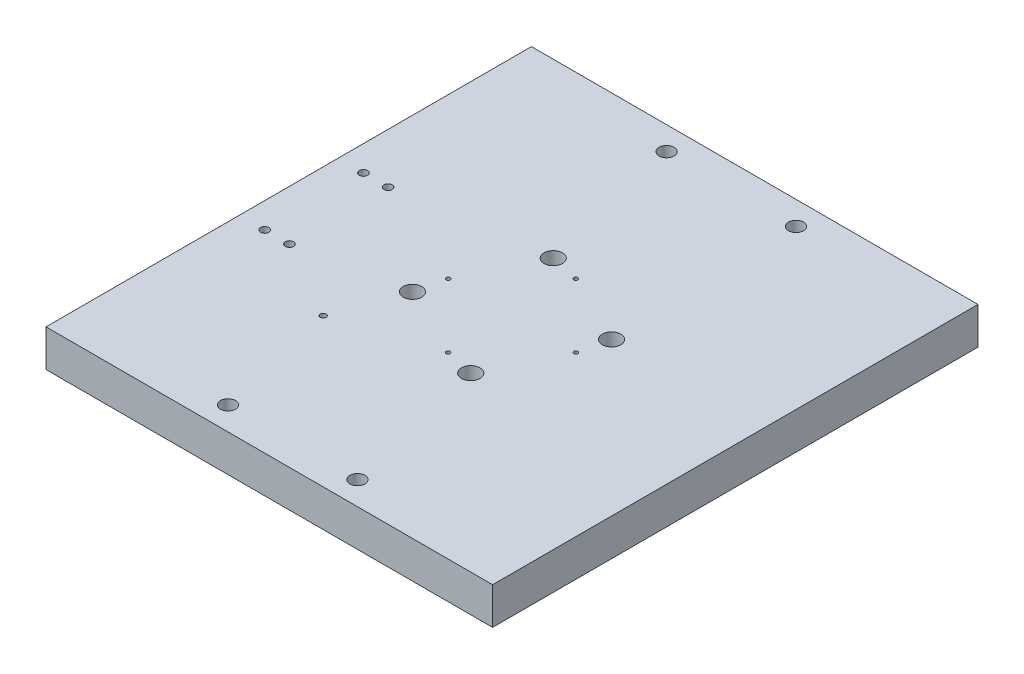
SolidWorks part; units mm, degrees
ref_plane "Front Plane" through (0, 0, 0) normal (0, 0, 1) x (1, 0, 0)
ref_plane "Top Plane" through (0, 0, 0) normal (0, 1, 0) x (1, 0, 0)
ref_plane "Right Plane" through (0, 0, 0) normal (1, 0, 0) x (0, 0, -1)
sketch "Sketch1" plane through (0, 0, 0) normal (0, 1, 0) x (1, 0, 0)
  line L1 (-230, -250) -> (230, -250)
  line L2 (-230, -250) -> (-230, 250)
  line L3 (-230, 250) -> (230, 250)
  line L4 (230, -250) -> (230, 250)
  line L5 (-230, -250) -> (230, 250) construction
  line L6 (-230, 250) -> (230, -250) construction
  point P0 (0, 0)
  dimension "D1" = 500
  dimension "D3" = 0
  dimension "D2" = 460
extrude "Boss-Extrude1" add sketch "Sketch1" along normal blind 38.1
sketch "Sketch3" plane through (0, 38.1, 0) normal (0, 1, 0) x (1, 0, 0)
  line L0 (-230, -250) -> (230, 250) construction
  line L1 (230, -250) -> (-230, 250) construction
  line L2 (0, 0) -> (225.0272, 0) construction
  line L3 (0, 0) -> (0, 160) construction
  line L4 (0, 0) -> (-160, 0) construction
  line L5 (145, 0) -> (145, -15) construction
  line L6 (-145, 0) -> (-145, -23.128) construction
  circle A0 centre (0, 0) radius 145
  circle A1 centre (0, 0) radius 130
  circle A2 centre (0, 0) radius 160
  arc A3 (-130, 0) -> (-160, 0) centre (-145, 0) cw
  arc A4 (130, 0) -> (160, 0) centre (145, 0) ccw
  point P19 (-145, -15)
  dimension "D1" = 15
  dimension "D2" = 15
sketch "Sketch5" plane through (0, 38.1, 0) normal (0, 1, 0) x (1, 0, 0)
  line L0 (65.786, 0) -> (-65.786, 0) construction
  line L1 (0, -124.9952) -> (0, 101.4653) construction
  circle A0 centre (0, 0) radius 65.786
  point P7 (0, -65.786)
  point P8 (0, 65.786)
  dimension "D1" = 131.572
hole_wizard "Tap Drill for M5x0.8 Tap1" positions "Sketch9" profile "Sketch8" hole size "M5x0.8" standard "ANSI Metric"
sketch "Sketch9" plane through (0, 38.1, 0) normal (0, 1, 0) x (1, 0, 0)
  point P0 (0, 65.786)
  point P3 (65.786, 0)
  point P6 (0, -65.786)
  point P9 (-65.786, 0)
sketch "Sketch8" plane through (0, 38.1, -65.786) normal (1, 0, 0) x (0, 0, 1)
  line L0 (0, 0) -> (0, 21.2618)
  line L1 (0, 21.2618) -> (2.1, 20)
  line L2 (2.1, 20) -> (2.1, 0)
  line L5 (2.1, 0) -> (0, 0)
  line L10 (0, 21.2618) -> (-2.1, 20) construction
  line L11 (0, -6.35) -> (0, 107.95) construction
  dimension "Hole Dia." = 4.2
  dimension "Hole Depth" = 20
  dimension "Drill Angle" = 118
sketch "Sketch10" plane through (0, 0, 0) normal (0, -1, 0) x (1, 0, 0)
  line L0 (-72.5116, 30.0353) -> (0, 0) construction
  line L1 (0, 0) -> (72.5116, -30.0353) construction
  line L2 (30.0353, 72.5116) -> (0, 0) construction
  line L3 (0, 0) -> (-30.0353, -72.5116) construction
  line L4 (0, 124.9952) -> (0, -101.4653) construction
  circle A0 centre (0, 0) radius 78.486
  point P3 (0, 78.486)
  point P4 (78.486, 0)
  point P5 (0, -78.486)
  point P6 (-78.486, 0)
  point P7 (-72.5116, 30.0353)
  point P9 (30.0353, 72.5116)
  dimension "D1" = 67.5
  dimension "D3" = 156.972
  dimension "D2" = 22.5
hole_wizard "3/4 (0.7500) Dowel Hole1" positions "Sketch12" profile "Sketch11" hole size "3/4" standard "ANSI Inch" end condition through all
sketch "Sketch12" plane through (0, 0, 0) normal (0, -1, 0) x (-1, 0, 0)
  point P0 (72.5116, -30.0353)
  point P3 (-30.0353, -72.5116)
  point P6 (30.0353, 72.5116)
  point P9 (-72.5116, 30.0353)
sketch "Sketch11" plane through (-72.5116, 0, 30.0353) normal (1, 0, 0) x (0, 0, -1)
  line L0 (0, 0) -> (0, 38.1)
  line L1 (0, 38.1) -> (9.525, 38.1)
  line L2 (9.525, 38.1) -> (9.525, 0)
  line L5 (9.525, 0) -> (0, 0)
  line L11 (0, -6.35) -> (0, 107.95) construction
  dimension "Thru Hole Dia." = 19.05
  dimension "Thru Hole Depth" = 38.1
sketch "Sketch13" plane through (0, 0, 0) normal (0, -1, 0) x (1, 0, 0)
  circle A0 centre (0, 0) radius 90
extrude "Cut-Extrude4" cut sketch "Sketch13" against normal blind 15
sketch "Sketch14" plane through (0, 38.1, 0) normal (0, 1, 0) x (1, 0, 0)
  line L0 (0, 250) -> (0, -273.069) construction
  line L1 (230, 250) -> (-230, 250) construction
  line L2 (0, -273.069) -> (0, -250) construction
  line L3 (-230, -250) -> (230, -250) construction
  line L4 (0, -250) -> (0, 250) construction
  line L7 (-230, -225.87) -> (230, -225.87) construction
  line L8 (-230, 250) -> (-230, -250) construction
  line L9 (230, -250) -> (230, 250) construction
  line L10 (-230, 225.87) -> (230, 225.87) construction
  point P5 (-66.67, 225.87)
  point P9 (66.67, 225.87)
  point P10 (-66.67, -225.87)
  point P11 (66.67, -225.87)
  dimension "D1" = 66.67
  dimension "D2" = 24.13
  dimension "D3" = 24.13
  dimension "D4" = 66.67
  dimension "D5" = 66.67
  dimension "D6" = 66.67
hole_wizard "M14 Clearance Hole1" positions "Sketch16" profile "Sketch15" hole size "M14" standard "ANSI Metric" end condition through all
sketch "Sketch16" plane through (0, 38.1, 0) normal (0, 1, 0) x (1, 0, 0)
  point P0 (66.67, -225.87)
  point P3 (-66.67, -225.87)
  point P6 (-66.67, 225.87)
  point P9 (66.67, 225.87)
sketch "Sketch15" plane through (66.67, 38.1, 225.87) normal (1, 0, 0) x (0, 0, 1)
  line L0 (0, 0) -> (0, 38.1)
  line L1 (0, 38.1) -> (7.75, 38.1)
  line L2 (7.75, 38.1) -> (7.75, 0)
  line L5 (7.75, 0) -> (0, 0)
  line L11 (0, -6.35) -> (0, 107.95) construction
  dimension "Thru Hole Dia." = 15.5
  dimension "Thru Hole Depth" = 38.1
sketch "Sketch18" plane through (0, 38.1, 0) normal (0, 1, 0) x (1, 0, 0)
  line L2 (-97.2272, -97.2272) -> (0, 0) construction
  line L3 (0, -124.9952) -> (0, 101.4653) construction
  point P0 (-97.2272, -97.2272)
  dimension "D1" = 137.5
  dimension "D2" = 45
sketch "Sketch23" plane through (0, 0, 0) normal (0, -1, 0) x (1, 0, 0)
  line L0 (-553.8, -76.2) -> (-153.8, -76.2) construction
  line L1 (-553.8, 76.2) -> (-153.8, 76.2) construction
  line L2 (-553.8, -76.2) -> (-153.8, -76.2)
  line L3 (-553.8, 76.2) -> (-153.8, 76.2)
  line L5 (-230, -250) -> (-230, 250) construction
  point P0 (-178.4381, 50.8)
  point P1 (-178.438, -50.8)
  point P3 (-203.838, -50.8)
  point P5 (-203.838, 50.8814)
  dimension "D2" = 25.4
  dimension "D3" = 26.162
  dimension "D4" = 25.4
  dimension "D6" = 26.162
  dimension "D7" = 25.4
hole_wizard "Tap Drill for M10x1.5 Tap1" positions "Sketch25" profile "Sketch26" hole size "M10x1.5" standard "ANSI Metric" end condition through all
sketch "Sketch25" plane through (0, 0, 0) normal (0, -1, 0) x (-1, 0, 0)
  point P0 (178.438, 50.8)
  point P3 (203.838, 50.8)
  point P6 (178.4381, -50.8)
  point P9 (203.838, -50.8814)
sketch "Sketch26" plane through (-178.438, 0, -50.8) normal (1, 0, 0) x (0, 0, -1)
  line L0 (0, 0) -> (0, 38.1)
  line L1 (0, 38.1) -> (4.25, 38.1)
  line L2 (4.25, 38.1) -> (4.25, 0)
  line L5 (4.25, 0) -> (0, 0)
  line L11 (0, -6.35) -> (0, 107.95) construction
  dimension "Thru Hole Dia." = 8.5
  dimension "Thru Hole Depth" = 38.1
hole_wizard "Ø6.0mm Dowel Hole1" positions "Sketch28" profile "Sketch27" hole size "Ø6.0" standard "ANSI Metric"
sketch "Sketch28" plane through (0, 38.1, 0) normal (0, 1, 0) x (1, 0, 0)
  point P0 (-97.2272, -97.2272)
sketch "Sketch27" plane through (-97.2272, 38.1, 97.2272) normal (1, 0, 0) x (0, 0, 1)
  line L0 (0, 0) -> (0, 11.8026)
  line L1 (0, 11.8026) -> (3, 10)
  line L2 (3, 10) -> (3, 0)
  line L5 (3, 0) -> (0, 0)
  line L10 (0, 11.8026) -> (-3, 10) construction
  line L11 (0, -6.35) -> (0, 107.95) construction
  dimension "Hole Dia." = 6
  dimension "Hole Depth" = 10
  dimension "Drill Angle" = 118
